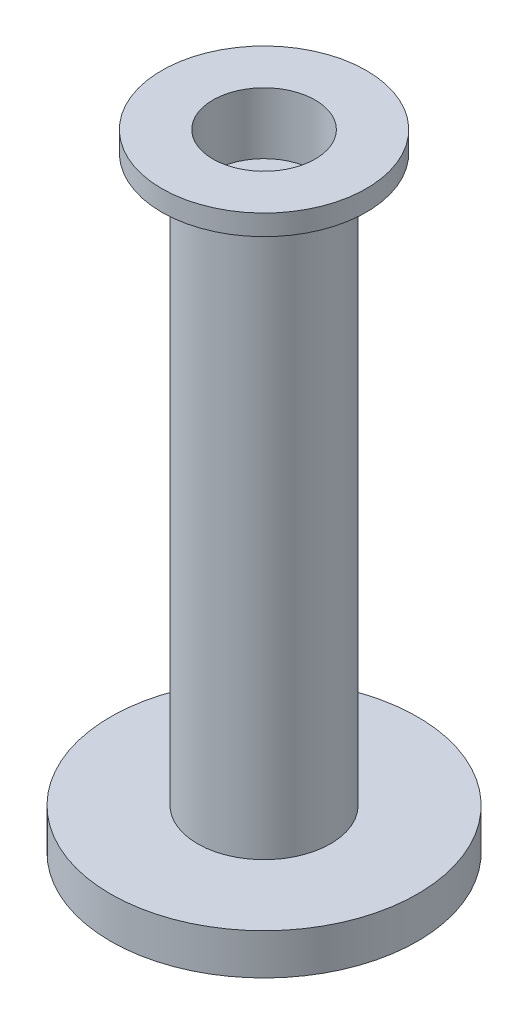
SolidWorks part; units mm, degrees
material "1023 Carbon Steel Sheet (SS)"
ref_plane "Front Plane" through (0, 0, 0) normal (0, 0, 1) x (1, 0, 0)
ref_plane "Top Plane" through (0, 0, 0) normal (0, 1, 0) x (1, 0, 0)
ref_plane "Right Plane" through (0, 0, 0) normal (1, 0, 0) x (0, 0, -1)
sketch "Sketch1" plane through (0, 0, 0) normal (0, 1, 0) x (1, 0, 0)
  circle A0 centre (0, 0) radius 3.75
  dimension "D1" = 7.5
extrude "Boss-Extrude1" add sketch "Sketch1" along normal blind 1
sketch "Sketch2" plane through (0, 1, 0) normal (0, 1, 0) x (1, 0, 0)
  circle A0 centre (0, 0) radius 1.625
  dimension "D1" = 3.25
extrude "Boss-Extrude2" add sketch "Sketch2" along normal blind 13.8
sketch "Sketch3" plane through (0, 14.8, 0) normal (0, 1, 0) x (1, 0, 0)
  circle A0 centre (0, 0) radius 2.5
  dimension "D1" = 5
extrude "Boss-Extrude3" add sketch "Sketch3" along normal blind 0.5
sketch "Sketch4" plane through (0, 15.3, 0) normal (0, 1, 0) x (1, 0, 0)
  circle A0 centre (0, 0) radius 1.25
  dimension "D1" = 2.5
extrude "Cut-Extrude2" cut sketch "Sketch4" against normal blind 1.5
